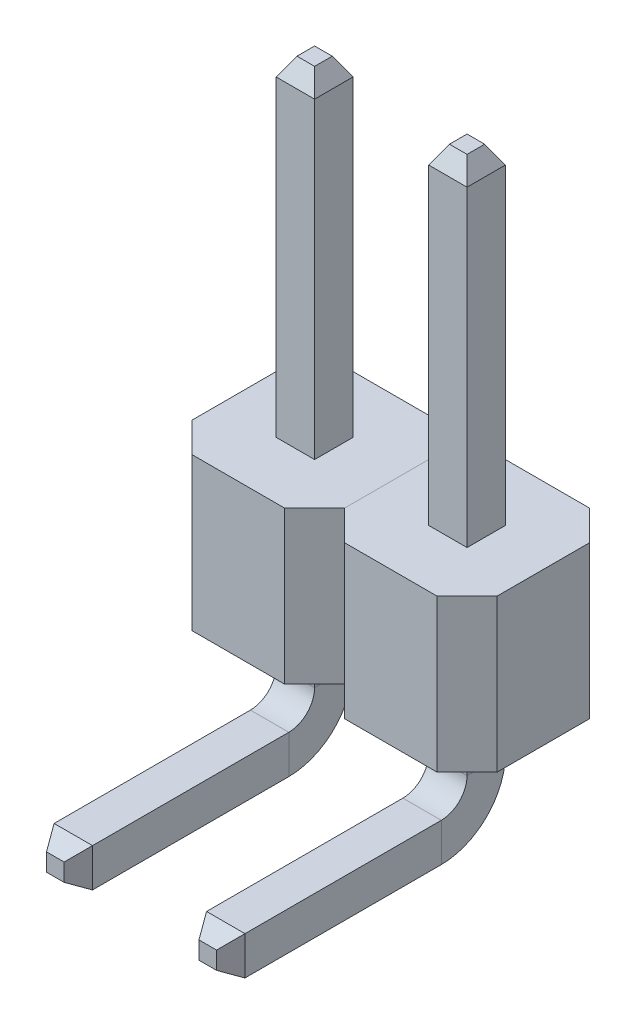
SolidWorks part; units mm, degrees
material "Male Header"
ref_plane "Front Plane" through (0, 0, 0) normal (0, 0, 1) x (1, 0, 0)
ref_plane "Top Plane" through (0, 0, 0) normal (0, 1, 0) x (1, 0, 0)
ref_plane "Right Plane" through (0, 0, 0) normal (1, 0, 0) x (0, 0, -1)
sketch "Sketch1" plane through (0, 0, 0) normal (0, 1, 0) x (1, 0, 0)
  line L1 (-1.27, -1.27) -> (1.27, -1.27)
  line L2 (-1.27, -1.27) -> (-1.27, 1.27)
  line L3 (-1.27, 1.27) -> (1.27, 1.27)
  line L4 (1.27, -1.27) -> (1.27, 1.27)
  line L5 (-1.27, -1.27) -> (1.27, 1.27) construction
  line L6 (-1.27, 1.27) -> (1.27, -1.27) construction
  point P0 (0, 0)
  dimension "D1" = 2.54
extrude "Boss-Extrude1" add sketch "Sketch1" along normal blind 2.54
chamfer "Chamfer1" distance 0.5 angle 45 4 edges at (-1.27, 1.27, -1.27) (-1.27, 1.27, 1.27) (1.27, 1.27, -1.27) (1.27, 1.27, 1.27)
sketch "Sketch2" plane through (0, 0, 0) normal (1, 0, 0) x (0, 0, -1)
  line L0 (0, 8.04) -> (0, -0.75)
  line L1 (-0.75, -1.5) -> (-4.32, -1.5)
  line L3 (-0.77, 2.54) -> (0.77, 2.54) construction
  line L4 (-1.27, 0) -> (-1.27, 2.54) construction
  arc A0 (0, -0.75) -> (-0.75, -1.5) centre (-0.75, -0.75) cw
  dimension "D2" = 0.75
  dimension "D1" = 1.5
  dimension "D3" = 5.5
  dimension "D4" = 3.05
sketch "Sketch3" plane through (0, 0, 0) normal (0, 1, 0) x (1, 0, 0)
  line L1 (-0.32, -0.32) -> (0.32, -0.32)
  line L2 (-0.32, -0.32) -> (-0.32, 0.32)
  line L3 (-0.32, 0.32) -> (0.32, 0.32)
  line L4 (0.32, -0.32) -> (0.32, 0.32)
  line L5 (-0.32, -0.32) -> (0.32, 0.32) construction
  line L6 (-0.32, 0.32) -> (0.32, -0.32) construction
  point P0 (0, 0)
  dimension "D1" = 0.64
sweep "Sweep1" add profiles "Sketch3" path "Sketch2"
chamfer "Chamfer2" distance 0.3 angle 30 8 edges at (0, -1.82, 4.32) (-0.32, -1.5, 4.32) (0, -1.18, 4.32) (0.32, -1.5, 4.32) (0, 8.04, 0.32) (-0.32, 8.04, 0) (0, 8.04, -0.32) (0.32, 8.04, 0)
pattern_linear "LPattern1" count 2 spacing 2.54 along (1, 0, 0) of bodies 102
pattern_linear "LPattern2" [suppressed] count 3 spacing 2.54
pattern_linear "LPattern3" [suppressed] count 4 spacing 2.54
pattern_linear "LPattern4" [suppressed] count 5 spacing 2.54
pattern_linear "LPattern5" [suppressed] count 6 spacing 2.54
